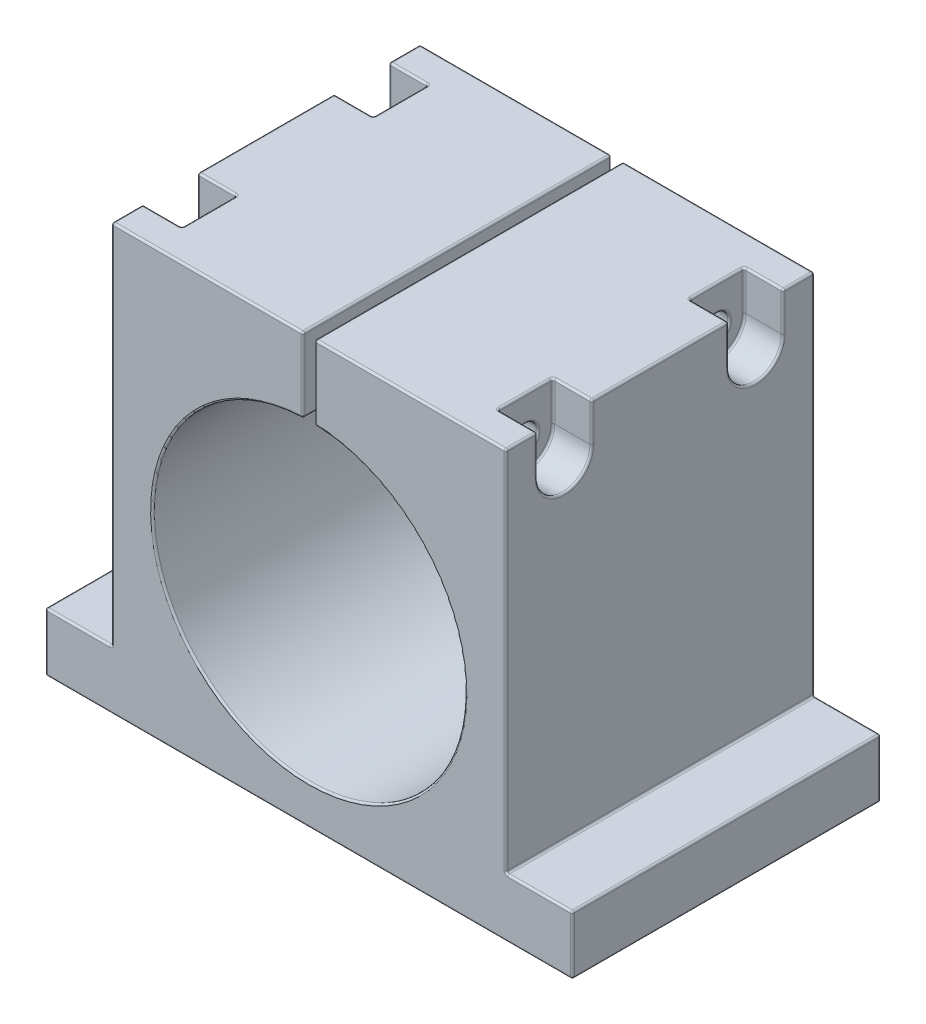
SolidWorks part; units mm, degrees
ref_plane "Спереди" through (0, 0, 0) normal (0, 0, 1) x (1, 0, 0)
ref_plane "Сверху" through (0, 0, 0) normal (0, 1, 0) x (1, 0, 0)
ref_plane "Справа" through (0, 0, 0) normal (1, 0, 0) x (0, 0, -1)
sketch "Эскиз1" plane through (0, 0, 0) normal (0, 0, 1) x (1, 0, 0)
  line L0 (158.9731, 494.9046) -> (1058.9731, 494.9046) construction
  line L1 (0, 0) -> (0, -50) construction
  line L2 (67.5, -50) -> (-67.5, -50)
  line L3 (-67.5, -50) -> (-67.5, -35)
  line L4 (-67.5, -35) -> (-50.5, -35)
  line L5 (-50.5, -35) -> (-50.5, 59)
  line L6 (-50.5, 59) -> (-1.5, 59)
  line L7 (-1.5, 59) -> (-1.5, 39.9719)
  line L8 (1.5, 59) -> (1.5, 39.9719)
  line L9 (50.5, 59) -> (1.5, 59)
  line L10 (50.5, -35) -> (50.5, 59)
  line L11 (67.5, -35) -> (50.5, -35)
  line L12 (67.5, -50) -> (67.5, -35)
  circle A0 centre (0, 0) radius 40
  dimension "D1" = 80
  dimension "D2" = 3
  dimension "D3" = 94
  dimension "D4" = 15
  dimension "D5" = 17
  dimension "D6" = 135
  dimension "D7" = 50
extrude "Бобышка-Вытянуть1" add sketch "Эскиз1" along normal mid plane 79 contours A0 L7 L6 L5 L4 L3 L2 L12 L11 L10 L9 L8
sketch "Эскиз2" plane through (-50.5, 0, 0) normal (-1, 0, 0) x (0, 0, 1)
  line L0 (39.5, 59) -> (-39.5, 59) construction
  line L1 (-31.5, 59) -> (-17.5, 59)
  line L2 (-31.5, 59) -> (-31.5, 49)
  line L3 (-31.5, 49) -> (-17.5, 49)
  line L4 (-17.5, 59) -> (-17.5, 49)
  line L5 (-39.5, -35) -> (-39.5, 59) construction
  line L6 (17.5, 59) -> (31.5, 59)
  line L7 (17.5, 59) -> (17.5, 49)
  line L8 (17.5, 49) -> (31.5, 49)
  line L9 (31.5, 59) -> (31.5, 49)
  line L10 (39.5, -35) -> (39.5, 59) construction
  circle A0 centre (-24.5, 49) radius 7
  circle A1 centre (24.5, 49) radius 7
  line M8 (39.5, 59) -> (-39.5, 59)
  dimension "D1" = 8
  dimension "D2" = 8
  dimension "D3" = 14
  dimension "D4" = 10
extrude "Вырез-Вытянуть1" cut sketch "Эскиз2" against normal blind 10 contours L3 A0 | A0 L4 L2 M8 | L8 A1 | L8 A1 | A1 L9 L7 M8
sketch "Эскиз3" plane through (50.5, 0, 0) normal (1, 0, 0) x (0, 0, -1)
  line L6 (-31.5, 59) -> (-31.5, 49)
  line L7 (-17.5, 59) -> (-31.5, 59)
  line L8 (-17.5, 49) -> (-17.5, 59)
  line L9 (-31.5, 59) -> (-31.5, 49)
  line L10 (-17.5, 59) -> (-31.5, 59)
  line L11 (-17.5, 49) -> (-17.5, 59)
  line L15 (17.5, 59) -> (17.5, 49)
  line L16 (31.5, 59) -> (17.5, 59)
  line L17 (31.5, 49) -> (31.5, 59)
  line L18 (17.5, 59) -> (17.5, 49)
  line L19 (31.5, 59) -> (17.5, 59)
  line L20 (31.5, 49) -> (31.5, 59)
  arc A2 (-31.5, 49) -> (-17.5, 49) centre (-24.5, 49) ccw
  arc A3 (-31.5, 49) -> (-17.5, 49) centre (-24.5, 49) ccw
  arc A5 (17.5, 49) -> (31.5, 49) centre (24.5, 49) ccw
  arc A6 (17.5, 49) -> (31.5, 49) centre (24.5, 49) ccw
  dimension "D1" = 0
  dimension "D2" = 0
extrude "Вырез-Вытянуть2" cut sketch "Эскиз3" against normal blind 10
sketch "Эскиз4" plane through (-40.5, 0, 0) normal (-1, 0, 0) x (0, 0, 1)
  circle A0 centre (-24.5, 49) radius 3.25
  circle A1 centre (24.5, 49) radius 3.25
  dimension "D1" = 6.5
  dimension "D2" = 6.5
extrude "Вырез-Вытянуть3" cut sketch "Эскиз4" against normal through all
fillet "Скругление1" radius 0.5 80 edges at (50.5, 54, -31.5) (50.5, 54, 31.5) (50.5, 42, 24.5) (50.5, 54, 17.5) (50.5, 54, -17.5) (50.5, 42, -24.5) (50.5, -35, 0) (1.5, 49.4859, 39.5) (50.5, 12, 39.5) (59, -35, 39.5) (0, -50, 39.5) (-1.5, 49.4859, 39.5) (-50.5, 54, 17.5) (-50.5, 42, 24.5) (-50.5, 54, 31.5) (-50.5, 12, 39.5) (-50.5, 54, -31.5) (-50.5, 42, -24.5) (-50.5, 54, -17.5) (-45.5, 59, -31.5) (-50.5, 59, -35.5) (-1.5, 59, 0) (-26, 59, 39.5) (-50.5, 59, 35.5) (-45.5, 59, 31.5) (-45.5, 59, 17.5) (-50.5, 59, 0) (-45.5, 59, -17.5) (45.5, 59, 17.5) (45.5, 59, 31.5) (50.5, 59, 35.5) (26, 59, 39.5) (1.5, 59, 0) (50.5, 59, -35.5) (45.5, 59, -31.5) (45.5, 59, -17.5) (50.5, 59, 0) (40.5, 54, -17.5) (40.5, 59, -24.5) (40.5, 54, -31.5) (40.5, 42, -24.5) (40.5, 52.25, -24.5) (40.5, 54, 31.5) (40.5, 59, 24.5) (40.5, 54, 17.5) (40.5, 42, 24.5) (40.5, 52.25, 24.5) (67.5, -50, 0) (67.5, -42.5, 39.5) (67.5, -35, 0) (1.5, 39.9719, 0) (0, -40, 39.5) (-1.5, 39.9719, 0) (-1.5, 49.4859, -39.5) (-26, 59, -39.5) (-50.5, 12, -39.5) (0, -50, -39.5) (67.5, -42.5, -39.5) (59, -35, -39.5) (50.5, 12, -39.5) (26, 59, -39.5) (1.5, 49.4859, -39.5) (0, -40, -39.5) (-67.5, -42.5, 39.5) (-67.5, -50, 0) (-67.5, -42.5, -39.5) (-50.5, -35, 0) (-59, -35, 39.5) (-67.5, -35, 0) (-59, -35, -39.5) (-40.5, 54, 17.5) (-40.5, 59, 24.5) (-40.5, 54, 31.5) (-40.5, 42, 24.5) (-40.5, 45.75, 24.5) (-40.5, 54, -31.5) (-40.5, 59, -24.5) (-40.5, 54, -17.5) (-40.5, 42, -24.5) (-40.5, 45.75, -24.5)
